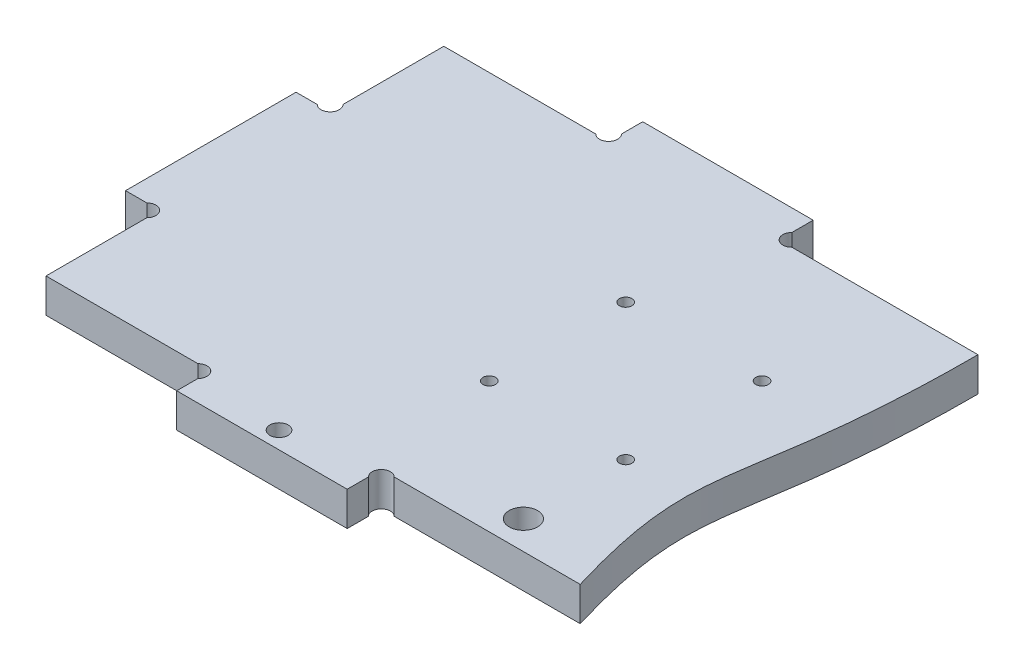
SolidWorks part; units mm, degrees
ref_plane "Plan de face" through (0, 0, 0) normal (0, 0, 1) x (1, 0, 0)
ref_plane "Plan de dessus" through (0, 0, 0) normal (0, 1, 0) x (1, 0, 0)
ref_plane "Plan de droite" through (0, 0, 0) normal (1, 0, 0) x (0, 0, -1)
sketch "Esquisse1" plane through (0, 0, 0) normal (0, 1, 0) x (1, 0, 0)
  line L0 (-17.765, 0) -> (149.6937, 0) construction
  line L1 (0, -38.2901) -> (0, 99.4612) construction
  line L2 (6, -24.7073) -> (6, 99.4612) construction
  line L3 (-17.765, 82) -> (149.6937, 82) construction
  line L4 (50, -24.7073) -> (50, 11) construction
  line L5 (122.0715, 6) -> (-6.878, 6) construction
  line L6 (35, 11.2969) -> (35, -24.7073) construction
  line L7 (100, 99.4612) -> (100, -38.2901) construction
  line L8 (-17.765, 41) -> (67.8794, 41) construction
  line L9 (-9.4628, 26) -> (28.156, 26) construction
  line L10 (35, 6) -> (19.0943, -9.9057) construction
  line L11 (6, 26) -> (-8.9691, 11.0309) construction
  line L12 (35, 3.7373) -> (35, 0)
  line L13 (35, 0) -> (65, 0)
  line L14 (65, 0) -> (65, 3.7373)
  line L15 (65, 82) -> (65, 78.2627)
  line L16 (35, 82) -> (65, 82)
  line L17 (35, 78.2627) -> (35, 82)
  line L18 (67.2627, 6) -> (100, 6)
  line L19 (32.7373, 6) -> (6, 6)
  line L20 (6, 6) -> (6, 23.7373)
  line L21 (3.7373, 26) -> (0, 26)
  line L22 (0, 26) -> (0, 56)
  line L23 (0, 56) -> (3.7373, 56)
  line L24 (6, 58.2627) -> (6, 76)
  line L25 (6, 76) -> (32.7373, 76)
  line L26 (67.2627, 76) -> (100, 76)
  line L27 (78.4129, 11) -> (122.0715, 11) construction
  line L28 (92.6412, 53) -> (52.2759, 53) construction
  line L29 (52.2759, 29) -> (92.6412, 29) construction
  line L30 (61, 65.9043) -> (61, 20.2646) construction
  line L31 (85, 57.1314) -> (85, 7.5703) construction
  line L32 (96, 87.4325) -> (96, -4.9233) construction
  line L33 (112.3395, 26) -> (94.5787, 26) construction
  line L34 (112.3395, 52) -> (94.5787, 52) construction
  line L35 (45.4898, 3) -> (80.6078, 3) construction
  arc A0 (35, 3.7373) -> (32.7373, 6) centre (33.8686, 4.8686) ccw
  arc A1 (6, 23.7373) -> (3.7373, 26) centre (4.8686, 24.8686) ccw
  arc A2 (65, 3.7373) -> (67.2627, 6) centre (66.1314, 4.8686) cw
  arc A3 (6, 58.2627) -> (3.7373, 56) centre (4.8686, 57.1314) cw
  arc A4 (65, 78.2627) -> (67.2627, 76) centre (66.1314, 77.1314) ccw
  arc A5 (35, 78.2627) -> (32.7373, 76) centre (33.8686, 77.1314) cw
  circle A6 centre (85, 53) radius 1.1
  circle A7 centre (61, 53) radius 1.1
  circle A8 centre (85, 29) radius 1.1
  circle A9 centre (61, 29) radius 1.1
  circle A10 centre (85, 11) radius 2.5
  circle A11 centre (50, 3) radius 1.6
  spline S0 degree 3 poles (100, 76) (100.0026, 33.8042) (90.8729, 36.4662) (100, 6) knots 0 0 0 0 1 1 1 1
  dimension "D17" = 30
  dimension "D18" = 5
  dimension "D10" = 45
  dimension "D12" = 24
  dimension "D11" = 24
  dimension "D16" = 4
  dimension "D14" = 55
  dimension "D19" = 3
  dimension "D1" = 6
  dimension "D2" = 82
  dimension "D3" = 29
  dimension "D4" = 6
  dimension "D5" = 100
  dimension "D6" = 15
  dimension "D7" = 41
  dimension "D8" = 15
  dimension "D9" = 45
  dimension "D13" = 12
  dimension "D15" = 20
extrude "Boss.-Extru.1" add sketch "Esquisse1" along normal blind 6
